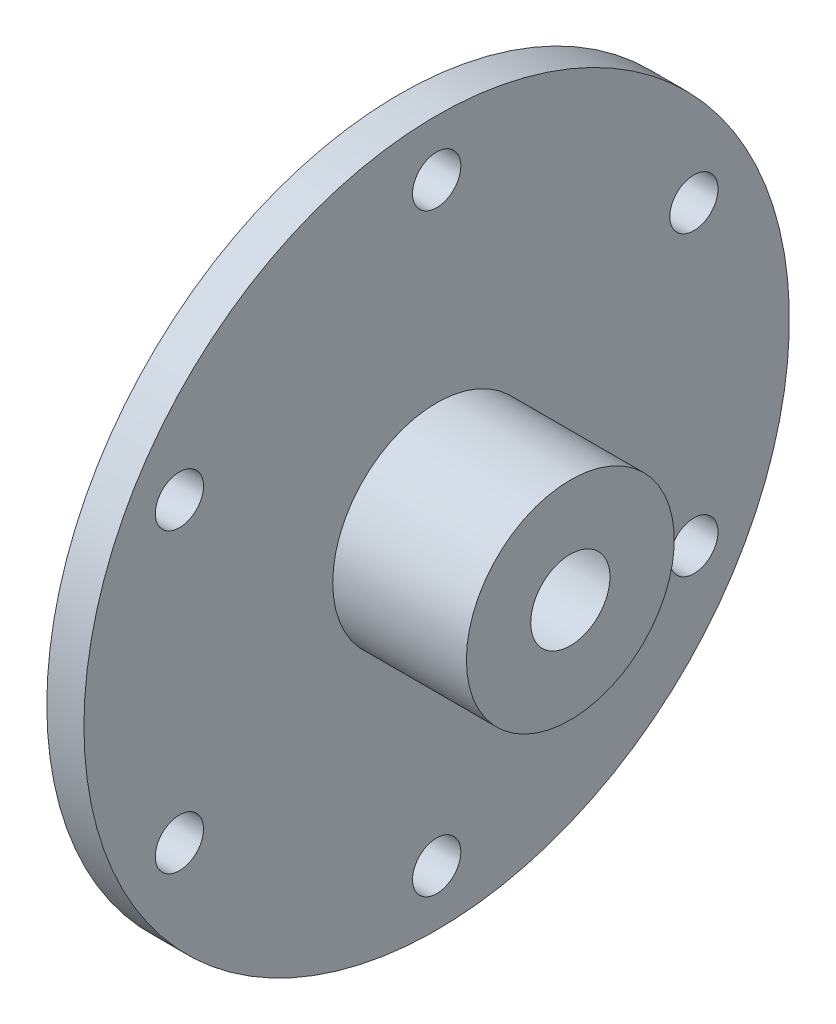
SolidWorks part; units mm, degrees
ref_plane "Front Plane" through (0, 0, 0) normal (0, 0, 1) x (1, 0, 0)
ref_plane "Top Plane" through (0, 0, 0) normal (0, 1, 0) x (1, 0, 0)
ref_plane "Right Plane" through (0, 0, 0) normal (1, 0, 0) x (0, 0, -1)
sketch "Sketch1" plane through (0, 0, 0) normal (0, 0, 1) x (1, 0, 0)
  line L0 (-20.0253, 0) -> (7.9747, 0) construction
  line L1 (-20.0253, 0) -> (-20.0253, 35)
  line L2 (-20.0253, 35) -> (-15.0253, 35)
  line L3 (-15.0253, 35) -> (-15.0253, 47.5)
  line L4 (-15.0253, 47.5) -> (-10.0253, 47.5)
  line L5 (-10.0253, 47.5) -> (-10.0253, 14)
  line L6 (-10.0253, 14) -> (7.9747, 14)
  line L7 (7.9747, 14) -> (7.9747, 0)
  line L8 (-20.0253, 0) -> (7.9747, 0)
  dimension "D1" = 35
  dimension "D2" = 5
  dimension "D3" = 5
  dimension "D4" = 47.5
  dimension "D5" = 14
  dimension "D6" = 28
revolve "Revolve1" add sketch "Sketch1" angle 360 about L0
hole_wizard "CSK for M12 Hex Socket Countersunk Cap Screw1" positions "Sketch6" profile "Sketch7" countersink size "M12" standard "ISO"
sketch "Sketch6" plane through (-20.0253, 0, 0) normal (-1, 0, 0) x (0, 0, 1)
  point P0 (0, 0)
sketch "Sketch7" plane through (-20.0253, 0, 0) normal (0, 1, 0) x (0, 0, 1)
  line L0 (0, 0) -> (0, 31.206)
  line L1 (0, 31.206) -> (7, 27)
  line L2 (7, 27) -> (7, 6)
  line L3 (7, 6) -> (13, 0)
  line L5 (13, 0) -> (0, 0)
  line L6 (-7, 6) -> (-13, 0) construction
  line L10 (0, 31.206) -> (-7, 27) construction
  line L11 (0, -6.35) -> (0, 107.95) construction
  dimension "Hole Dia." = 14
  dimension "Hole Depth" = 27
  dimension "Near C'Sink Dia." = 26
  dimension "Near C'Sink Angle" = 90
  dimension "Drill Angle" = 118
sketch "Sketch8" plane through (-10.0253, 0, 0) normal (1, 0, 0) x (0, 0, -1)
  circle A0 centre (0, 0) radius 40 construction
  dimension "D1" = 80
sketch "Sketch10" plane through (-20.0253, 0, 0) normal (-1, 0, 0) x (0, 0, 1)
  line L0 (0, -51.6182) -> (0, 57.9763) construction
  circle A0 centre (0, 0) radius 40 construction
  point P7 (0, 40)
  dimension "D1" = 80
hole_wizard "CSK for M6 Hex Socket Countersunk Cap Screw1" positions "Sketch10" profile "Sketch12" countersink size "M6" standard "ISO" end condition through all
sketch "Sketch12" plane through (-20.0253, 40, 0) normal (0, 1, 0) x (0, 0, 1)
  line L0 (0, 0) -> (0, 28)
  line L1 (0, 28) -> (3.25, 28)
  line L2 (3.25, 28) -> (3.25, 0.5)
  line L3 (3.25, 0.5) -> (3.75, 0)
  line L5 (3.75, 0) -> (0, 0)
  line L6 (-3.25, 0.5) -> (-3.75, 0) construction
  line L11 (0, -6.35) -> (0, 107.95) construction
  dimension "Thru Hole Dia." = 6.5
  dimension "Thru Hole Depth" = 28
  dimension "Near C'Sink Dia." = 7.5
  dimension "Near C'Sink Angle" = 90
pattern_circular "CirPattern1" count 6 over 360 about axis through (0, 0, 0) along (1, 0, 0) of "CSK for M6 Hex Socket Countersunk Cap Screw1"
